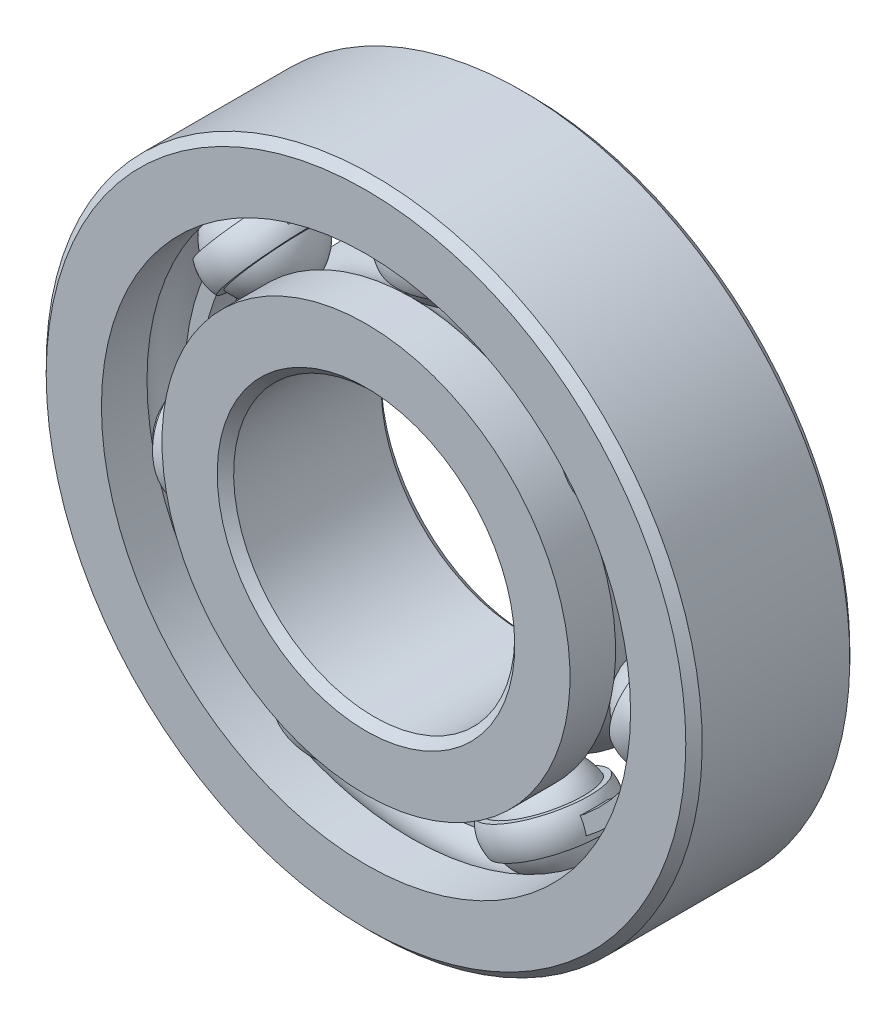
SolidWorks part; units mm, degrees
ref_plane "Front Plane" through (0, 0, 0) normal (0, 0, 1) x (1, 0, 0)
ref_plane "Top Plane" through (0, 0, 0) normal (0, 1, 0) x (1, 0, 0)
ref_plane "Right Plane" through (0, 0, 0) normal (1, 0, 0) x (0, 0, -1)
sketch "Sketch1" plane through (0, 0, 0) normal (0, 0, 1) x (1, 0, 0)
  line L0 (-11.1125, 0) -> (11.1125, 0) construction
  line L1 (-4.7625, 0) -> (4.7625, 0) construction
  circle A0 centre (0, 0) radius 4.7625 construction
  circle A1 centre (0, 0) radius 11.1125 construction
  point P3 (0, 0)
  point P6 (0, 0)
  point P7 (0, -4.7625)
  point P11 (0, -11.1125)
  point P12 (0, 4.7625)
  point P13 (0, 11.1125)
  dimension "OD" = 22.225
  dimension "ID" = 9.525
sketch "SketchB" plane through (0, 0, 0) normal (1, 0, 0) x (0, 0, -1)
  line L0 (-2.7781, 11.1125) -> (2.7781, 11.1125) construction
  line L1 (0, 11.1125) -> (0, -11.1125) construction
  line L2 (2.5003, 11.1125) -> (-2.5003, 11.1125)
  line L3 (-2.5003, 11.1125) -> (-2.7781, 10.8347)
  line L4 (-2.7781, 10.8347) -> (-2.7781, 8.9633)
  line L5 (-2.7781, 8.9633) -> (-1.2347, 8.9633)
  line L6 (2.7781, 8.9633) -> (1.2347, 8.9633)
  line L7 (2.7781, 10.8347) -> (2.7781, 8.9633)
  line L8 (2.5003, 11.1125) -> (2.7781, 10.8347)
  line L9 (0, 11.1125) -> (0, 7.9375) construction
  line L10 (0, 7.9375) -> (0, 4.7625) construction
  line L11 (0, 11.1125) -> (0, -11.1125) construction
  line L12 (-2.7781, 0) -> (2.7781, 0) construction
  line L13 (2.7781, 4.7625) -> (-2.7781, 4.7625) construction
  line L14 (0, 9.5427) -> (0, 6.3323) construction
  line L15 (-2.7781, -4.7625) -> (2.7781, -4.7625) construction
  arc A0 (-1.2347, 8.9633) -> (1.2347, 8.9633) centre (0, 7.9375) cw
  circle A1 centre (0, 7.9375) radius 1.6052 construction
  point P14 (0, 4.7625)
  point P17 (0, 0)
  point P21 (0, 11.1125)
  point P29 (0, 4.7625)
  point P30 (0, -4.7625)
  point P35 (0, 9.5427)
  dimension "Width" = 5.5562
  dimension "D1" = 45
  dimension "D2" = 0.2778
  dimension "D3" = 2.4694
  dimension "D4" = 1.0258
sketch "Sketch7" plane through (0, 0, 0) normal (1, 0, 0) x (0, 0, -1)
  line L0 (2.5003, 11.1125) -> (2.7781, 10.8347) construction
  line L1 (2.7781, 10.8347) -> (2.7781, 8.9633) construction
  line L2 (2.7781, 8.9633) -> (1.2347, 8.9633) construction
  line L3 (-2.7781, 8.9633) -> (-1.2347, 8.9633) construction
  line L4 (-2.7781, 10.8347) -> (-2.7781, 8.9633) construction
  line L5 (-2.5003, 11.1125) -> (-2.7781, 10.8347) construction
  line L6 (2.5003, 11.1125) -> (-2.5003, 11.1125) construction
  line L7 (2.5003, 11.1125) -> (2.7781, 10.8347)
  line L8 (2.7781, 10.8347) -> (2.7781, 8.9633)
  line L9 (2.7781, 8.9633) -> (1.2347, 8.9633)
  line L10 (-2.7781, 8.9633) -> (-1.2347, 8.9633)
  line L11 (-2.7781, 10.8347) -> (-2.7781, 8.9633)
  line L12 (-2.5003, 11.1125) -> (-2.7781, 10.8347)
  line L13 (2.5003, 11.1125) -> (-2.5003, 11.1125)
  arc A0 (1.2347, 8.9633) -> (-1.2347, 8.9633) centre (0, 7.9375) ccw construction
  arc A1 (1.2347, 8.9633) -> (-1.2347, 8.9633) centre (0, 7.9375) ccw
revolve "Revolve6" add sketch "Sketch7" angle 360 about L12
sketch "Sketch3" plane through (0, 0, 0) normal (1, 0, 0) x (0, 0, -1)
  line L0 (0, 11.1125) -> (0, -11.1125) construction
  line L1 (0, 11.1125) -> (0, -11.1125) construction
  line L2 (-2.5003, 4.7625) -> (-2.7781, 5.0403)
  line L3 (-2.7781, 5.0403) -> (-2.7781, 6.9117)
  line L5 (-2.7781, 6.9117) -> (-1.2347, 6.9117)
  line L6 (-2.5003, 4.7625) -> (2.5003, 4.7625)
  line L8 (2.5003, 4.7625) -> (2.7781, 5.0403)
  line L10 (2.7781, 5.0403) -> (2.7781, 6.9117)
  line L11 (2.7781, 6.9117) -> (1.2347, 6.9117)
  line L12 (-2.7781, 10.8347) -> (-2.7781, 8.9633) construction
  line L13 (2.5003, 11.1125) -> (2.7781, 10.8347) construction
  line L15 (2.7781, -10.8347) -> (2.7781, 10.8347) construction
  line L16 (2.5003, 11.1125) -> (2.5003, -11.1125) construction
  arc A1 (1.2347, 6.9117) -> (-1.2347, 6.9117) centre (0, 7.9375) cw
  circle A2 centre (0, 7.9375) radius 1.6052 construction
  point P1 (0, 4.7625)
revolve "Revolve3" add sketch "Sketch3" angle 360 about L12
sketch "Sketch4" plane through (0, 0, 0) normal (1, 0, 0) x (0, 0, -1)
  line L0 (-1.6052, 7.9375) -> (1.6052, 7.9375)
  arc A2 (-1.6052, 7.9375) -> (1.6052, 7.9375) centre (0, 7.9375) cw
  arc A3 (1.2347, 8.9633) -> (-1.2347, 8.9633) centre (0, 7.9375) ccw construction
revolve "Revolve4" add sketch "Sketch4" angle 360 about L0
sketch "Sketch8" plane through (0, 0, 0) normal (1, 0, 0) x (0, 0, -1)
  line L0 (-1.2347, 8.9633) -> (-1.2347, 8.4504) construction
  line L1 (-1.2347, 8.4504) -> (-1.2347, 7.9375) construction
  line L2 (-1.2347, 7.9375) -> (-1.2347, 7.4246) construction
  line L3 (-1.2347, 7.4246) -> (-1.2347, 6.9117) construction
  line L4 (-2.7781, 8.4504) -> (-2.5686, 8.4504) construction
  line L5 (-1.2347, 8.4504) -> (-1.2347, 7.4246) construction
  line L7 (-2.5686, 8.4504) -> (-2.3591, 8.4504) construction
  line L8 (-2.3591, 8.4504) -> (-2.1496, 8.4504) construction
  line L10 (0, 11.1125) -> (0, -11.1125) construction
  line L11 (0, 11.1125) -> (0, -11.1125) construction
  line L12 (-2.7781, 8.9633) -> (-2.7781, 8.4504) construction
  line L13 (-1.7306, 8.4504) -> (-1.5211, 8.4504) construction
  line L14 (-2.7781, 10.8347) -> (-2.7781, -10.8347) construction
  line L15 (-2.7781, 8.4504) -> (-2.7781, 7.9375) construction
  line L16 (-2.7781, 7.9375) -> (-2.7781, 7.4246) construction
  line L17 (-2.7781, 7.4246) -> (-2.7781, 6.9117) construction
  line L18 (-2.1496, 8.4504) -> (-1.9401, 8.4504) construction
  line L19 (-1.9401, 8.4504) -> (-1.7306, 8.4504) construction
  line L20 (-1.5211, 8.4504) -> (-1.7306, 8.4504)
  line L21 (-2.7781, 7.4246) -> (-2.5686, 7.4246) construction
  line L22 (-2.5686, 7.4246) -> (-2.3591, 7.4246) construction
  line L23 (-2.3591, 7.4246) -> (-2.1496, 7.4246) construction
  line L24 (-2.1496, 7.4246) -> (-1.9401, 7.4246) construction
  line L25 (-1.9401, 7.4246) -> (-1.7306, 7.4246) construction
  line L26 (-1.7306, 7.4246) -> (-1.5211, 7.4246) construction
  line L27 (-1.5211, 7.4246) -> (-1.7306, 7.4246)
  line L28 (-1.9401, 8.4504) -> (-1.9401, 7.4246) construction
  line L30 (-1.8353, 8.4504) -> (-1.8353, 7.4246) construction
  circle A0 centre (0, 7.9375) radius 1.6052 construction
  arc A2 (-1.7306, 7.4246) -> (-1.7306, 8.4504) centre (-0.5274, 7.9375) cw
  arc A3 (-1.5211, 8.4504) -> (-1.5211, 7.4246) centre (0, 7.9375) ccw
revolve "Revolve7" add sketch "Sketch8" angle 360 about L11
pattern_circular "CirPattern1" count 7 over 360 about axis through (0, 0, 0) along (0, 0, 1) of bodies 134 104
sketch "Sketch9" plane through (0, 0, 0) normal (0, 0, 1) x (1, 0, 0)
  line L0 (0, 6.9117) -> (0, 7.2537) construction
  line L1 (0, 6.3323) -> (0, 9.5427) construction
  line L2 (0, 7.2537) -> (0, 7.5956) construction
  line L3 (0, 7.5956) -> (0, 7.9375) construction
  line L4 (0, 7.9375) -> (0, 8.2794) construction
  line L5 (0, 8.2794) -> (0, 8.6213) construction
  line L6 (0, 8.6213) -> (0, 8.9633) construction
  line L7 (0, 10.8347) -> (0, 8.9633) construction
  line L8 (0, 11.1125) -> (0, -11.1125) construction
  circle A0 centre (0, 0) radius 6.9117 construction
  circle A1 centre (0, 0) radius 7.9375
  circle A2 centre (0, 0) radius 8.4504
  point P19 (0, 8.4504)
extrude "Boss-Extrude1" add sketch "Sketch9" along normal mid plane 0.926 separate body
equation "\"D2@SketchB\" = \"Width@SketchB\" * .05"
equation "\"D3@SketchB\" = \"Width@SketchB\" / 2.25"
equation "\"D4@SketchB\" =  (  (  ( \"OD@Sketch1\" - \"Width@SketchB\" )  / 2 )  / 3.25 )  / 2.5"
equation "\"D1@Boss-Extrude1\"=\"Width@SketchB\"/6"
